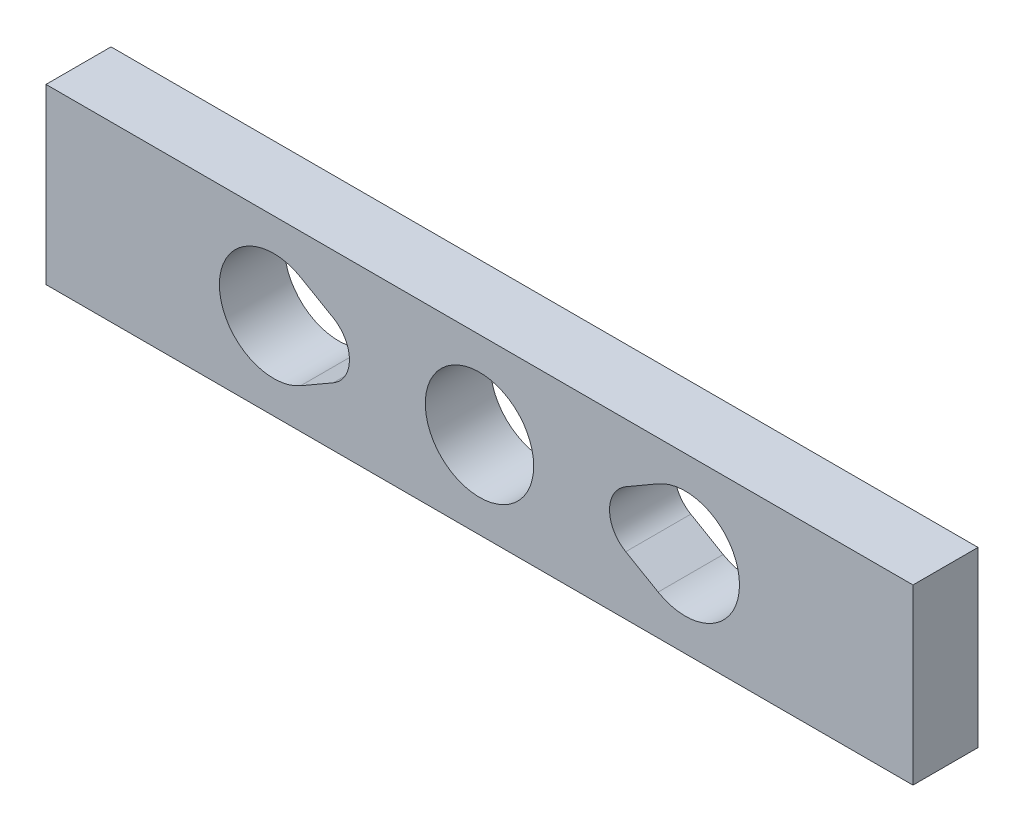
SolidWorks part; units mm, degrees
material "Balsa"
ref_plane "Front Plane" through (0, 0, 0) normal (0, 0, 1) x (1, 0, 0)
ref_plane "Top Plane" through (0, 0, 0) normal (0, 1, 0) x (1, 0, 0)
ref_plane "Right Plane" through (0, 0, 0) normal (1, 0, 0) x (0, 0, -1)
sketch "Sketch1" plane through (0, 0, 0) normal (0, 0, 1) x (1, 0, 0)
  line L0 (-6.7463, 2.2999) -> (-8.2463, 3.1659)
  line L1 (20.0037, 5.0008) -> (-19.9963, 5.0008)
  line L2 (20.0037, 5.0008) -> (20.0037, -2.9992)
  line L3 (20.0037, -2.9992) -> (-19.9963, -2.9992)
  line L4 (-19.9963, 5.0008) -> (-19.9963, -2.9992)
  line L5 (-19.9963, -2.9992) -> (20.0037, -2.9992)
  line L6 (-9.4963, 1.0008) -> (9.4992, 1.0008) construction
  line L7 (-6.7463, -0.2982) -> (-8.2463, -1.1642)
  line L8 (8.2477, 3.1651) -> (6.752, 2.2989)
  line L9 (8.2463, -1.1626) -> (6.752, -0.2972)
  circle A0 centre (0.0037, 1.0008) radius 2.5
  arc A1 (-6.7463, -0.2982) -> (-6.7463, 2.2999) centre (-7.4963, 1.0008) ccw
  arc A2 (6.752, 2.2989) -> (6.752, -0.2972) centre (7.5037, 1.0008) ccw
  arc A3 (11.9866, 1.2508) -> (8.2449, 3.1634) centre (9.4992, 1.0008) ccw
  arc A4 (-11.9838, 0.7508) -> (-8.2463, -1.1642) centre (-9.4963, 1.0008) ccw
  arc A5 (-11.9838, 1.2508) -> (-11.9838, 0.7508) centre (-9.4963, 1.0008) ccw
  arc A6 (11.9866, 1.2508) -> (11.9866, 0.7508) centre (9.4992, 1.0008) cw
  arc A7 (-8.2463, 3.1659) -> (-11.9838, 1.2508) centre (-9.4963, 1.0008) ccw
  arc A8 (8.2463, -1.1626) -> (11.9866, 0.7508) centre (9.4992, 1.0008) ccw
  dimension "D1" = 5
  dimension "D2" = 18.9955
  dimension "D5" = 0
  dimension "D7" = 9.5
  dimension "D8" = 20
  dimension "D9" = 3
  dimension "D10" = 3
  dimension "D11" = 15
  dimension "D3" = 8
  dimension "D4" = 4
  dimension "D6" = 40
extrude "Boss-Extrude1" add sketch "Sketch1" along normal blind 3 contours L1 L4 L3 L2 A0 A5 A4 A3 A6
